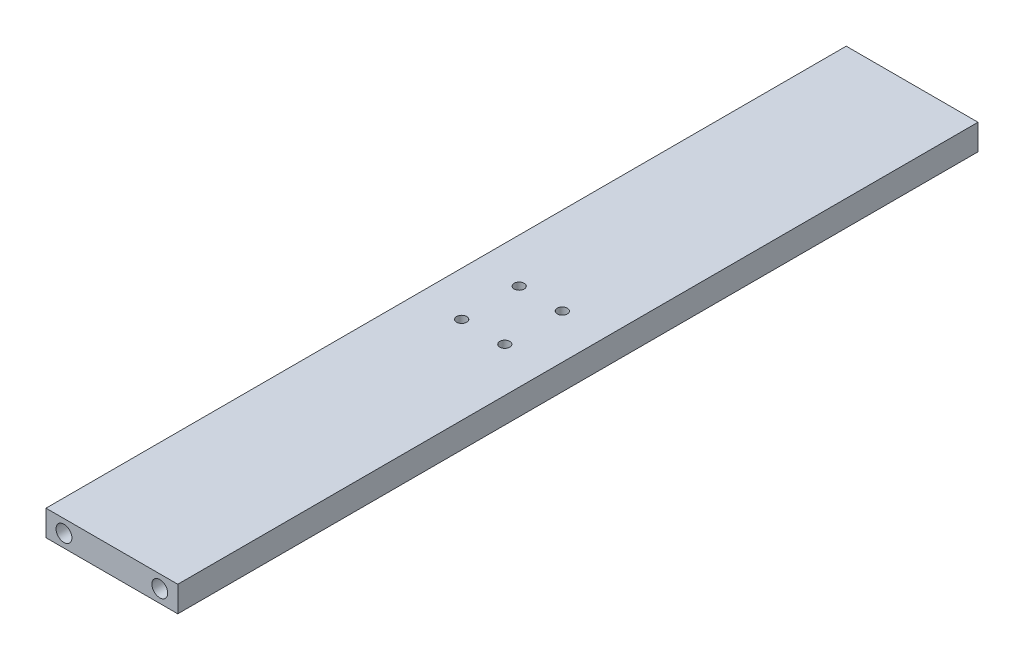
SolidWorks part; units mm, degrees
ref_plane "Plano frontal" through (0, 0, 0) normal (0, 0, 1) x (1, 0, 0)
ref_plane "Plano superior" through (0, 0, 0) normal (0, 1, 0) x (1, 0, 0)
ref_plane "Plano direito" through (0, 0, 0) normal (1, 0, 0) x (0, 0, -1)
sketch "Esboço1" plane through (0, 0, 0) normal (0, 0, 1) x (1, 0, 0)
  line L1 (27.5, -5.35) -> (-27.5, -5.35)
  line L2 (27.5, -5.35) -> (27.5, 5.35)
  line L3 (27.5, 5.35) -> (-27.5, 5.35)
  line L4 (-27.5, -5.35) -> (-27.5, 5.35)
  line L5 (27.5, -5.35) -> (-27.5, 5.35) construction
  line L6 (27.5, 5.35) -> (-27.5, -5.35) construction
  point P0 (0, 0)
  dimension "D1" = 55
  dimension "D2" = 10.7
extrude "Ressalto-extrusão1" add sketch "Esboço1" along normal blind 334
hole_wizard "Furo roscado para conduíte de M4x0.71" positions "Esboço5" profile "Esboço6" tap size "M4x0.7" standard "Helicoil® Metric" end condition through all
sketch "Esboço5" plane through (0, -5.35, 0) normal (0, -1, 0) x (-1, 0, 0)
  line L0 (35.9252, -167) -> (-60.6825, -167) construction
  line L2 (0, 17.4851) -> (0, -380.2509) construction
  line L4 (27.5, -334) -> (27.5, 0) construction
  line L5 (27.5, 0) -> (-27.5, 0) construction
  point P0 (9, -155)
  point P16 (0, 0)
  point P17 (-9, -155)
  point P18 (0, 0)
  point P19 (-9, -179)
  point P20 (9, -179)
  dimension "D1" = 18.5
  dimension "D2" = 155
sketch "Esboço6" plane through (-9, -5.35, 155) normal (1, 0, 0) x (0, 0, -1)
  line L0 (0, 0) -> (0, 10.7)
  line L1 (0, 10.7) -> (2.1, 10.7)
  line L2 (2.1, 10.7) -> (2.1, 0)
  line L5 (2.1, 0) -> (0, 0)
  line L11 (0, -6.35) -> (0, 107.95) construction
  dimension "Thru Tap Drill Dia." = 4.2
  dimension "Thru Tap Drill Depth" = 10.7
cosmetic thread "Rosca de furo1" parameters "D1"=15, "D2"=5.007
cosmetic thread "Rosca de furo2" parameters "D1"=15, "D2"=5.007
cosmetic thread "Rosca de furo3" parameters "D1"=15, "D2"=5.007
cosmetic thread "Rosca de furo4" parameters "D1"=15, "D2"=5.007
hole_wizard "Furo roscado para conduíte de 1/4-281" positions "Esboço8" profile "Esboço7" tap size "1/4-28" standard "Helicoil® Inch"
sketch "Esboço8" plane through (0, 0, 334) normal (0, 0, 1) x (1, 0, 0)
  line L0 (0, -9.0613) -> (0, 12.189) construction
  line L2 (31.5534, 0) -> (-32.8413, 0) construction
  line L4 (-27.5, 5.35) -> (-27.5, -5.35) construction
  point P0 (-20, 0)
  point P13 (0, 0)
  point P14 (20, 0)
  dimension "D1" = 7.5
sketch "Esboço7" plane through (-20, 0, 334) normal (1, 0, 0) x (0, -1, 0)
  line L0 (0, 0) -> (0, 16.9917)
  line L1 (0, 16.9917) -> (3.3147, 15)
  line L2 (3.3147, 15) -> (3.3147, 0)
  line L5 (3.3147, 0) -> (0, 0)
  line L10 (0, 16.9917) -> (-3.3147, 15) construction
  line L11 (0, -6.35) -> (0, 107.95) construction
  dimension "Tap Drill Dia." = 6.6294
  dimension "Tap Drill Depth" = 15
  dimension "Drill Angle" = 118
cosmetic thread "Rosca de furo5" parameters "D1"=15, "D2"=7.6073
cosmetic thread "Rosca de furo6" parameters "D1"=15, "D2"=7.6073
hole_wizard "Furo roscado para conduíte de 1/4-282" positions "Esboço9" profile "Esboço10" tap size "1/4-28" standard "Helicoil® Inch"
sketch "Esboço9" plane through (0, 0, 0) normal (0, 0, -1) x (-1, 0, 0)
  line L0 (0, 0) -> (0, 17.3255) construction
  line L2 (34.043, 0) -> (-41.338, 0) construction
  line L4 (-27.5, -5.35) -> (-27.5, 5.35) construction
  point P0 (-20, 0)
  point P12 (0, 0)
  point P15 (0, 0)
  point P16 (20, 0)
  dimension "D1" = 7.5
sketch "Esboço10" plane through (20, 0, 0) normal (1, 0, 0) x (0, 1, 0)
  line L0 (0, 0) -> (0, 16.9917)
  line L1 (0, 16.9917) -> (3.3147, 15)
  line L2 (3.3147, 15) -> (3.3147, 0)
  line L5 (3.3147, 0) -> (0, 0)
  line L10 (0, 16.9917) -> (-3.3147, 15) construction
  line L11 (0, -6.35) -> (0, 107.95) construction
  dimension "Tap Drill Dia." = 6.6294
  dimension "Tap Drill Depth" = 15
  dimension "Drill Angle" = 118
cosmetic thread "Rosca de furo7" parameters "D1"=15, "D2"=7.6073
cosmetic thread "Rosca de furo8" parameters "D1"=15, "D2"=7.6073
